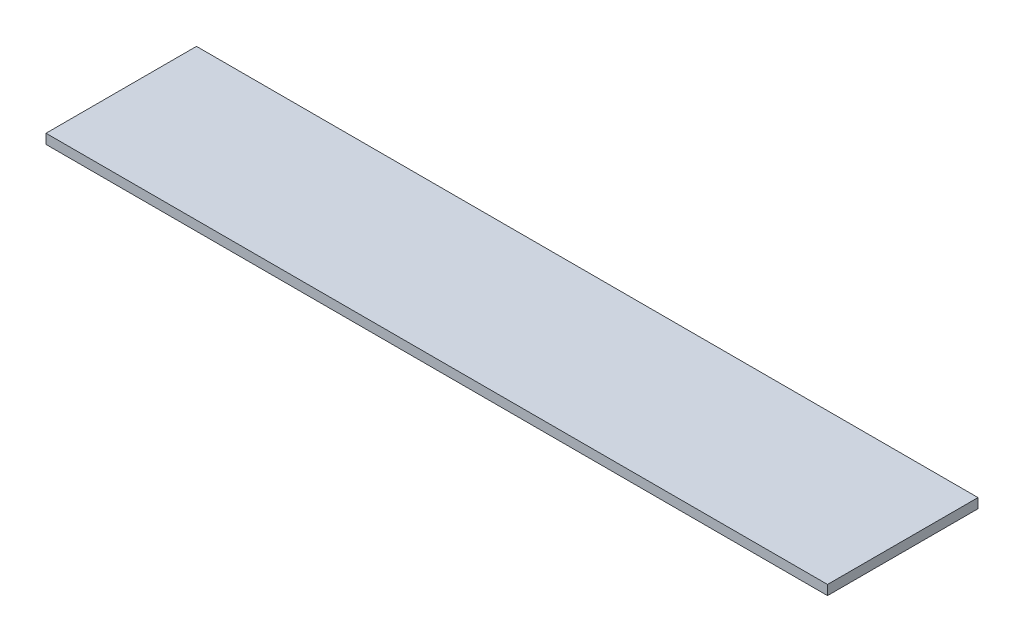
SolidWorks part; units mm, degrees
ref_plane "Front Plane" through (0, 0, 0) normal (0, 0, 1) x (1, 0, 0)
ref_plane "Top Plane" through (0, 0, 0) normal (0, 1, 0) x (1, 0, 0)
ref_plane "Right Plane" through (0, 0, 0) normal (1, 0, 0) x (0, 0, -1)
sketch "Sketch1" plane through (0, 0, 0) normal (0, 1, 0) x (1, 0, 0)
  line L1 (0, 0) -> (511.175, 0)
  line L2 (0, 0) -> (0, 98.425)
  line L3 (0, 98.425) -> (511.175, 98.425)
  line L4 (511.175, 0) -> (511.175, 98.425)
  dimension "D1" = 98.425
  dimension "D2" = 511.175
extrude "Boss-Extrude1" add sketch "Sketch1" along normal blind 6.35
